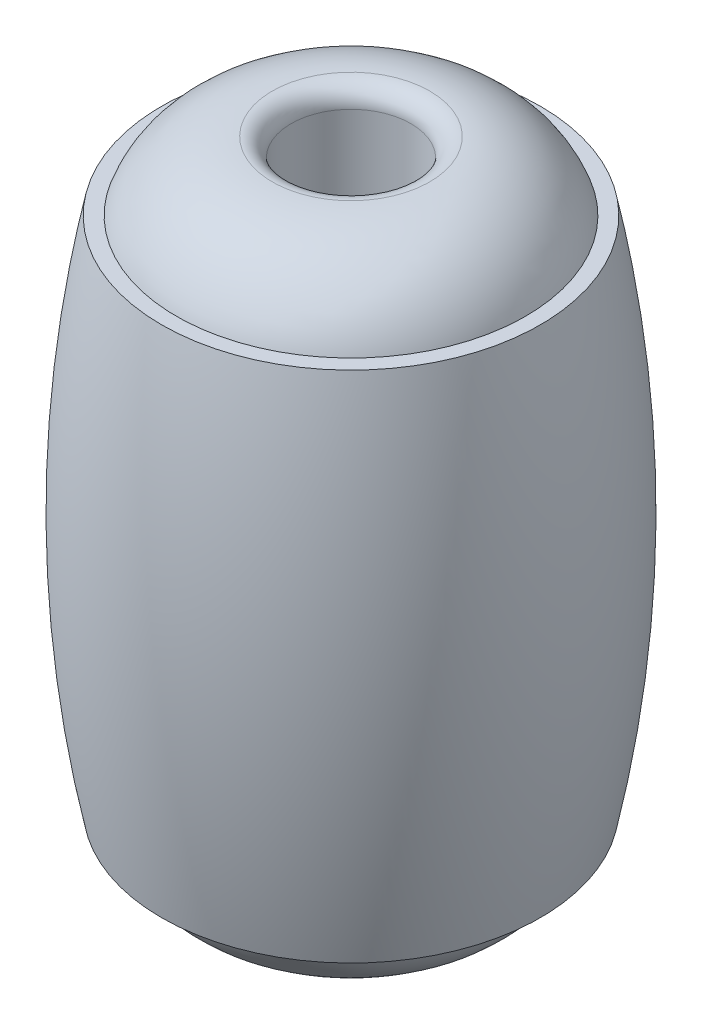
SolidWorks part; units mm, degrees
ref_plane "Front Plane" through (0, 0, 0) normal (0, 0, 1) x (1, 0, 0)
ref_plane "Top Plane" through (0, 0, 0) normal (0, 1, 0) x (1, 0, 0)
ref_plane "Right Plane" through (0, 0, 0) normal (1, 0, 0) x (0, 0, -1)
sketch "Sketch1" plane through (0, 0, 0) normal (0, 0, 1) x (1, 0, 0)
  line L0 (0, 0) -> (0, 7365.8324) construction
  line L1 (1.75, 0) -> (6.3, 0)
  line L2 (5.5319, 7.5) -> (5.1, 7.5)
  line L4 (1.75, 8.95) -> (1.75, 0)
  arc A0 (6.3, 0) -> (5.5319, 7.5) centre (-30.7, 0) ccw
  arc A1 (5.1, 7.5) -> (2.3, 9.5) centre (2.3, 6.54) ccw
  arc A2 (2.3, 9.5) -> (1.75, 8.95) centre (2.3, 8.95) ccw
  dimension "D3" = 37
  dimension "D1" = 6.3
  dimension "D2" = 7.5
  dimension "D4" = 5.1
  dimension "D5" = 2.3
  dimension "D6" = 9.5
  dimension "D7" = 1.75
revolve "Revolve1" add sketch "Sketch1" angle 360 about L0
mirror "Mirror1" about plane through (1.75, 0, 0) normal (0, -1, 0) of "Revolve1"
